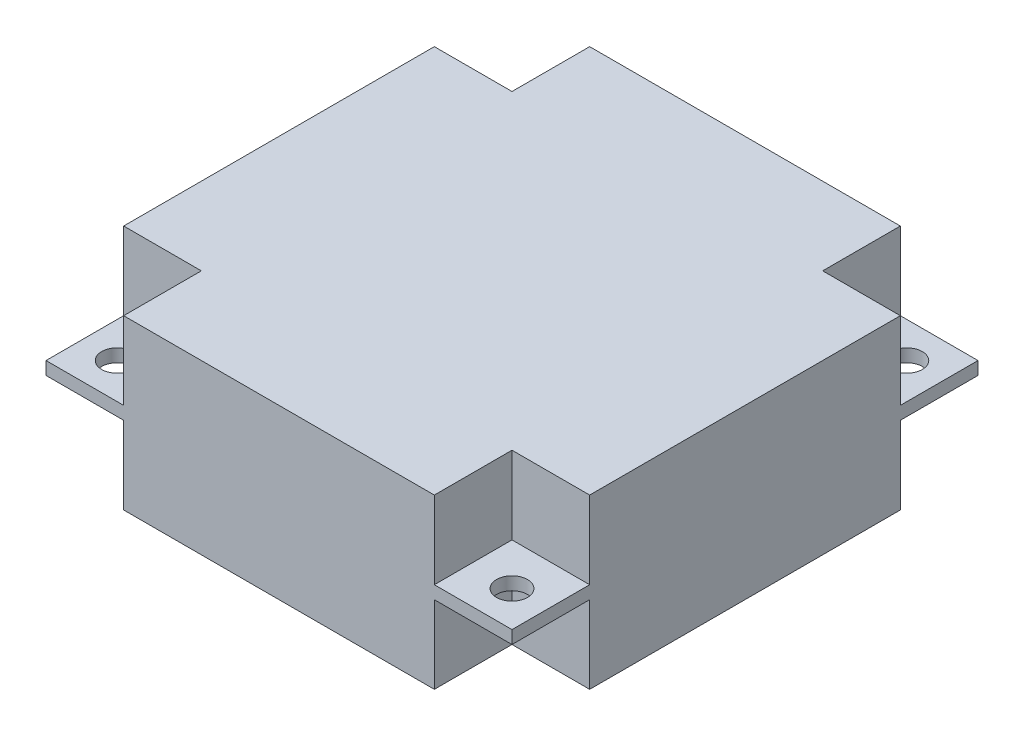
SolidWorks part; units mm, degrees
ref_plane "Plan de face" through (0, 0, 0) normal (0, 0, 1) x (1, 0, 0)
ref_plane "Plan de dessus" through (0, 0, 0) normal (0, 1, 0) x (1, 0, 0)
ref_plane "Plan de droite" through (0, 0, 0) normal (1, 0, 0) x (0, 0, -1)
sketch "Esquisse1" plane through (0, 0, 0) normal (0, 1, 0) x (1, 0, 0)
  line L1 (0, 0) -> (36, 0)
  line L2 (0, 0) -> (0, 36)
  line L3 (0, 36) -> (36, 36)
  line L4 (36, 0) -> (36, 36)
  dimension "D1" = 36
  dimension "D2" = 36
extrude "Boss.-Extru.1" add sketch "Esquisse1" along normal blind 1
hole_wizard "Dégagement M21" positions "Esquisse2" profile "Esquisse4" size "M2" standard "ISO" slot yes end condition through all
sketch "Esquisse2" plane through (0, 1, 0) normal (0, 1, 0) x (1, 0, 0)
  line L0 (0, 36) -> (0, 0) construction
  line L1 (0, 0) -> (36, 0) construction
  line L2 (36, 0) -> (36, 36) construction
  line L3 (36, 36) -> (0, 36) construction
  point P0 (2.75, 2.75)
  point P2 (2.75, 33.25)
  point P4 (33.25, 33.25)
  point P6 (33.25, 2.75)
  dimension "D1" = 2.75
  dimension "D2" = 2.75
  dimension "D3" = 2.75
  dimension "D4" = 2.75
  dimension "D5" = 2.75
  dimension "D6" = 2.75
  dimension "D7" = 2.75
  dimension "D8" = 2.75
sketch "Esquisse4" plane through (2.75, 1, -2.75) normal (1, 0, 0) x (0, 0, 1)
  line L0 (0, 0) -> (0, 1)
  line L1 (0, 1) -> (1.2, 1)
  line L2 (1.2, 1) -> (1.2, 0)
  line L5 (1.2, 0) -> (0, 0)
  line L11 (0, -6.35) -> (0, 107.95) construction
  dimension "Diamètre du perçage jusqu'au prochain" = 2.4
  dimension "Profondeur du perçage jusqu'au prochain" = 1
sketch "Esquisse5" plane through (0, 1, 0) normal (0, 1, 0) x (1, 0, 0)
  line L0 (0, 0) -> (36, 0) construction
  line L1 (6, 0) -> (30, 0)
  line L2 (6, 0) -> (6, 36)
  line L3 (6, 36) -> (30, 36)
  line L4 (30, 0) -> (30, 36)
  line L5 (36, 36) -> (0, 36) construction
  line L6 (36, 0) -> (36, 36) construction
  line L7 (36, 30) -> (0, 30)
  line L8 (36, 30) -> (36, 6)
  line L9 (36, 6) -> (0, 6)
  line L10 (0, 30) -> (0, 6)
  line L11 (0, 36) -> (0, 0) construction
  line M10 (0, 36) -> (0, 0)
  line M11 (0, 0) -> (36, 0)
  line M12 (36, 0) -> (36, 36)
  line M13 (36, 36) -> (0, 36)
  dimension "D1" = 6
  dimension "D2" = 6
  dimension "D3" = 6
  dimension "D4" = 6
extrude "Boss.-Extru.2" add sketch "Esquisse5" along normal blind 6 and the other way blind 7 contours L9 L2 L7 M10 | L9 L4 L7 L2 | L7 L4 L2 M13 | L9 L7 L4 M12 | L4 L9 L2 M11
